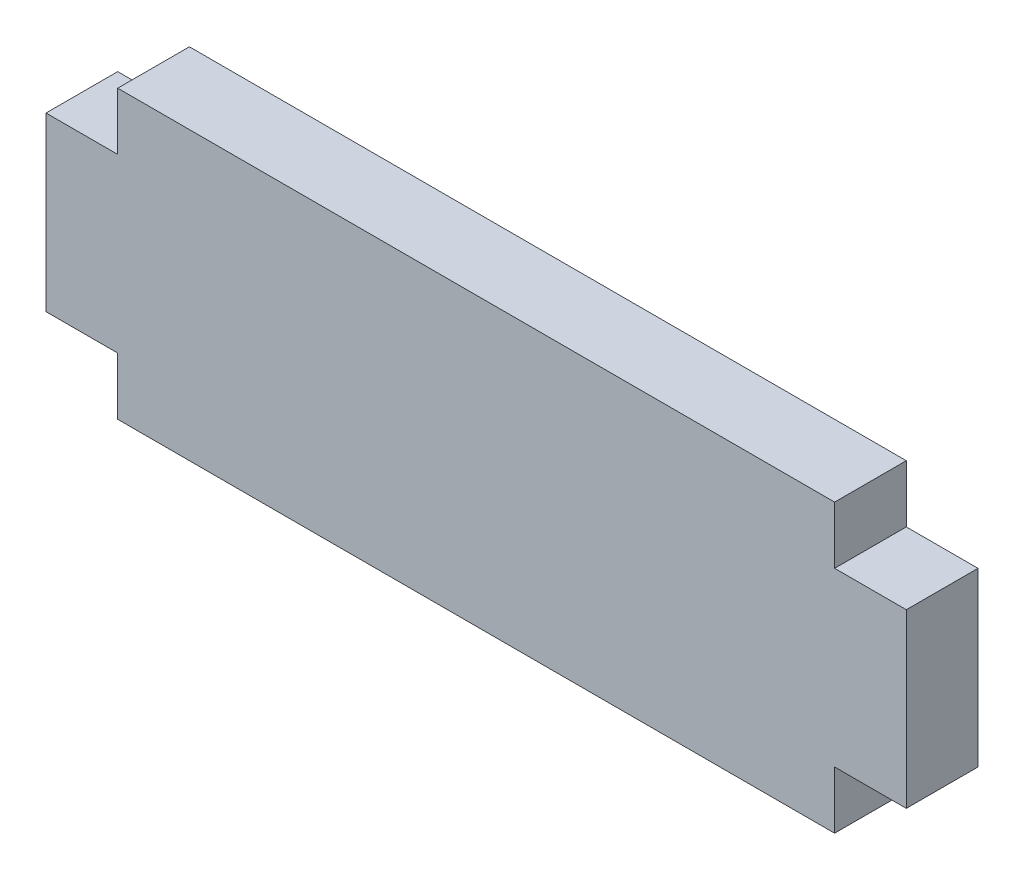
SolidWorks part; units mm, degrees
ref_plane "Front Plane" through (0, 0, 0) normal (0, 0, 1) x (1, 0, 0)
ref_plane "Top Plane" through (0, 0, 0) normal (0, 1, 0) x (1, 0, 0)
ref_plane "Right Plane" through (0, 0, 0) normal (1, 0, 0) x (0, 0, -1)
sketch "Sketch1" plane through (0, 0, 0) normal (0, 0, 1) x (1, 0, 0)
  line L1 (0, 0) -> (31.75, 0)
  line L2 (0, 0) -> (0, 12.7)
  line L3 (0, 12.7) -> (31.75, 12.7)
  line L4 (31.75, 0) -> (31.75, 12.7)
  dimension "D1" = 31.75
  dimension "D2" = 12.7
extrude "Boss-Extrude1" add sketch "Sketch1" along normal blind 3.175
sketch "Sketch2" plane through (0, 0, 3.175) normal (0, 0, 1) x (1, 0, 0)
  line L0 (0, 12.7) -> (0, 0) construction
  line L1 (0, 10.16) -> (-3.175, 10.16)
  line L2 (0, 10.16) -> (0, 2.54)
  line L3 (0, 2.54) -> (-3.175, 2.54)
  line L4 (-3.175, 10.16) -> (-3.175, 2.54)
  line L5 (15.875, 12.7) -> (15.875, 0) construction
  line L6 (31.75, 12.7) -> (0, 12.7) construction
  line L7 (0, 0) -> (31.75, 0) construction
  line L8 (31.75, 2.54) -> (34.925, 2.54)
  line L9 (31.75, 10.16) -> (31.75, 2.54)
  line L10 (31.75, 10.16) -> (34.925, 10.16)
  line L11 (34.925, 10.16) -> (34.925, 2.54)
  point P6 (0, 6.35)
  point P7 (-3.175, 6.35)
  dimension "D1" = 7.62
  dimension "D2" = 3.175
extrude "Boss-Extrude2" add sketch "Sketch2" against normal blind 3.175
